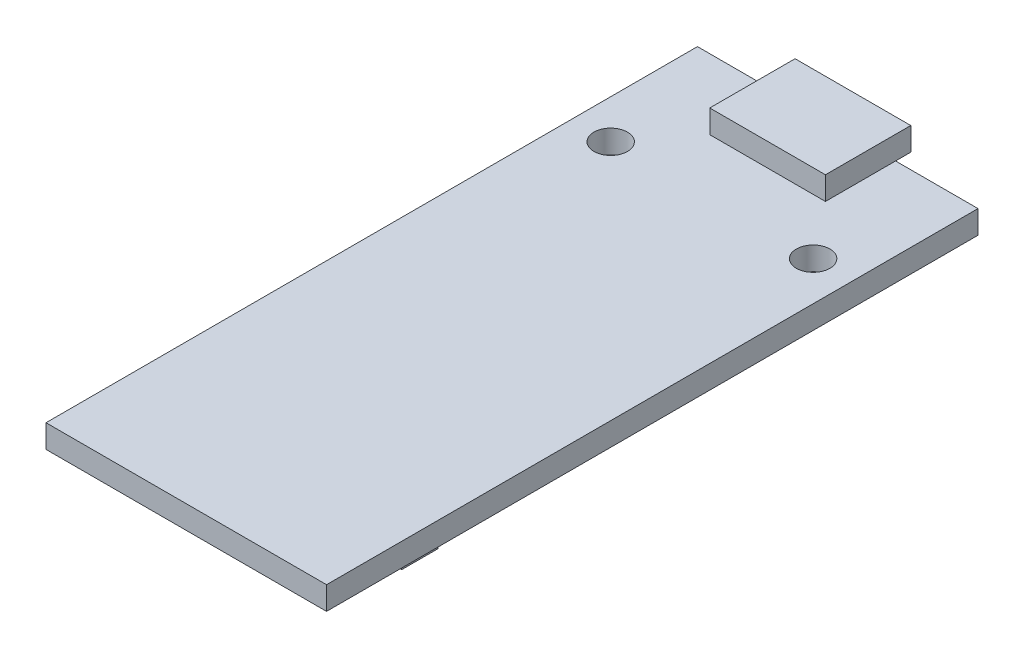
SolidWorks part; units mm, degrees
ref_plane "Front" through (0, 0, 0) normal (0, 0, 1) x (1, 0, 0)
ref_plane "Top" through (0, 0, 0) normal (0, 1, 0) x (1, 0, 0)
ref_plane "Right" through (0, 0, 0) normal (1, 0, 0) x (0, 0, -1)
sketch "Sketch1" plane through (0, 0, 0) normal (0, 1, 0) x (1, 0, 0)
  line L0 (0, -50) -> (0, 50) construction
  line L1 (-19.4, 0) -> (0, 0)
  line L2 (-19.4, 0) -> (-19.4, -45.05)
  line L3 (-19.4, -45.05) -> (0, -45.05)
  line L4 (0, 0) -> (0, -45.05)
  line L5 (-50, 0) -> (50, 0) construction
  dimension "D1" = 45.05
  dimension "D2" = 19.4
extrude "Boss-Extrude1" add sketch "Sketch1" along normal blind 1.6
sketch "Sketch2" plane through (0, 1.6, 0) normal (0, 1, 0) x (1, 0, 0)
  line L0 (-9.7, 1.05) -> (-9.7, 0) construction
  line L1 (-5.7, 1.05) -> (-13.7, 1.05)
  line L2 (-5.7, 1.05) -> (-5.7, -4.85)
  line L3 (-5.7, -4.85) -> (-13.7, -4.85)
  line L4 (-13.7, 1.05) -> (-13.7, -4.85)
  line L5 (0, 0) -> (-19.4, 0) construction
  dimension "D1" = 8
  dimension "D2" = 1.05
  dimension "D3" = 5.9
extrude "Boss-Extrude2" add sketch "Sketch2" along normal blind 1.6
sketch "Sketch3" plane through (0, 0, 0) normal (0, 1, 0) x (1, 0, 0)
  line L0 (-2.7, -8.7) -> (-16.7, -8.7) construction
  line L3 (0, 0) -> (-19.4, 0) construction
  line L4 (-9.7, -8.7) -> (-9.7, 0) construction
  circle A0 centre (-16.7, -8.7) radius 1.16
  circle A1 centre (-2.7, -8.7) radius 1.16
  point P4 (-9.7, -8.7)
  dimension "D1" = 2.32
  dimension "D2" = 14
  dimension "D3" = 8.7
extrude "Cut-Extrude3" cut sketch "Sketch3" along normal through all
sketch "Sketch4" plane through (0, 0, 0) normal (0, -1, 0) x (1, 0, 0)
  line L0 (-2.7, 8.7) -> (-16.7, 8.7) construction
  line L1 (-17.9, 12.87) -> (-10.65, 12.87)
  line L2 (-17.9, 12.87) -> (-17.9, 15.37)
  line L3 (-17.9, 15.37) -> (-10.65, 15.37)
  line L4 (-10.65, 12.87) -> (-10.65, 15.37)
  line L5 (-9.7, 35.8564) -> (-9.7, 0) construction
  line L7 (-17.9, 35.8564) -> (-1.5, 35.8564)
  line L8 (-17.9, 35.8564) -> (-17.9, 38.3564)
  line L9 (-17.9, 38.3564) -> (-1.5, 38.3564)
  line L10 (-1.5, 35.8564) -> (-1.5, 38.3564)
  line L11 (0, 0) -> (-19.4, 0) construction
  line L12 (-19.4, 0) -> (-19.4, 45.05) construction
  point P4 (-17.9, 14.12)
  point P9 (-14.275, 15.37)
  point P14 (-9.7, 35.8564)
  dimension "D1" = 2.5
  dimension "D2" = 5.42
  dimension "D3" = 7.25
  dimension "D4" = 1.5
  dimension "D5" = 2.5
extrude "Boss-Extrude3" add sketch "Sketch4" along normal blind 1.6
